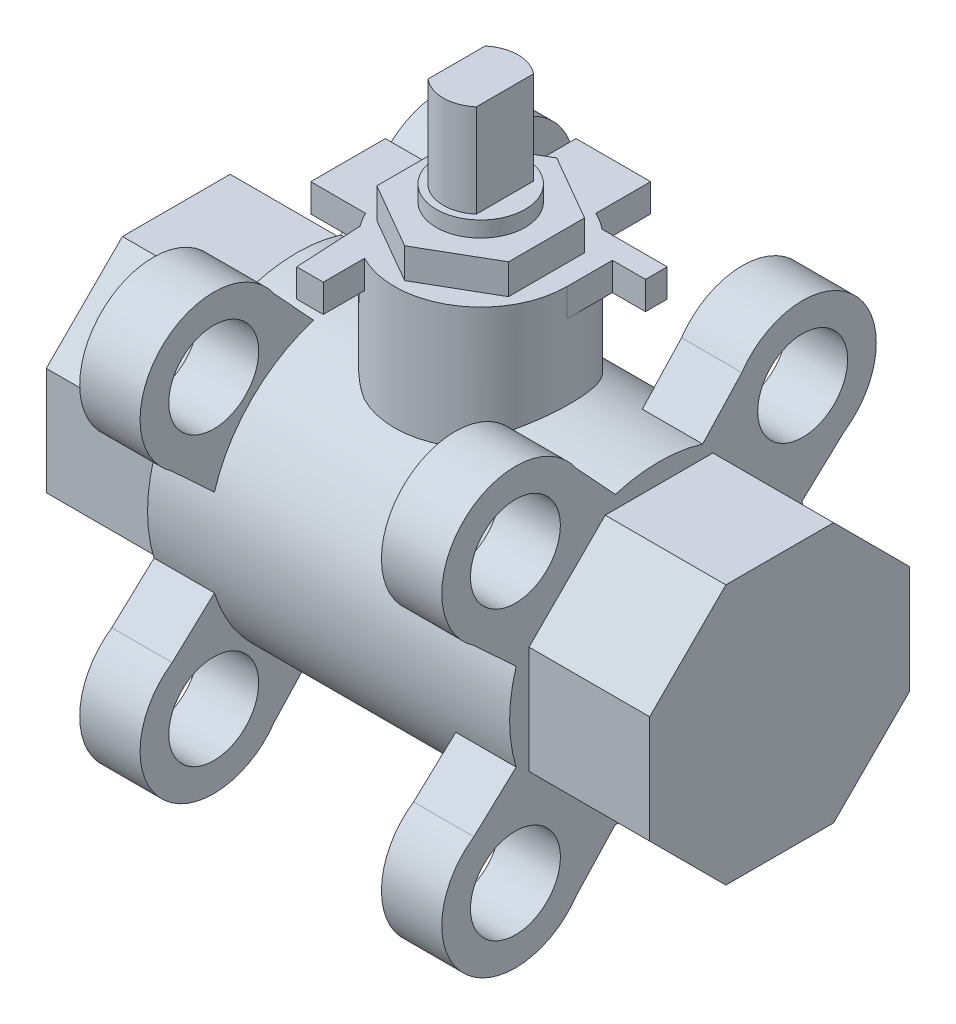
SolidWorks part; units mm, degrees
ref_plane "Front Plane" through (0, 0, 0) normal (0, 0, 1) x (1, 0, 0)
ref_plane "Top Plane" through (0, 0, 0) normal (0, 1, 0) x (1, 0, 0)
ref_plane "Right Plane" through (0, 0, 0) normal (1, 0, 0) x (0, 0, -1)
sketch "Sketch1" plane through (0, 0, 0) normal (1, 0, 0) x (0, 0, -1)
  line L0 (0, 0) -> (0, 26.4768) construction
  line L1 (0, 0) -> (0, -33.4304) construction
  line L2 (-12.3067, 12.3067) -> (-19.0868, 19.0868) construction
  line L3 (-19.4818, 8.7154) -> (-15.0368, 4.5929)
  line L4 (-20.0742, 0) -> (0, 0) construction
  line L5 (0, 0) -> (30.2419, 0) construction
  line L6 (19.4818, 8.7154) -> (15.0368, 4.5929)
  line L7 (8.7154, 19.4818) -> (4.5929, 15.0368)
  line L8 (19.4818, -8.7154) -> (15.0368, -4.5929)
  line L9 (8.7154, -19.4818) -> (4.5929, -15.0368)
  line L10 (-8.7154, 19.4818) -> (-4.5929, 15.0368)
  line L11 (-8.7154, -19.4818) -> (-4.5929, -15.0368)
  line L12 (-19.4818, -8.7154) -> (-15.0368, -4.5929)
  circle A0 centre (-15.113, 15.113) radius 4.7308
  arc A1 (-15.0368, -4.5929) -> (-15.0368, 4.5929) centre (0, 0) cw
  arc A2 (-8.7154, 19.4818) -> (-19.4818, 8.7154) centre (-15.113, 15.113) ccw
  arc A3 (4.5929, 15.0368) -> (-4.5929, 15.0368) centre (0, 0) ccw
  arc A4 (15.0368, -4.5929) -> (15.0368, 4.5929) centre (0, 0) ccw
  circle A5 centre (15.113, 15.113) radius 4.7308
  arc A6 (8.7154, 19.4818) -> (19.4818, 8.7154) centre (15.113, 15.113) cw
  circle A7 centre (15.113, -15.113) radius 4.7307
  arc A8 (8.7154, -19.4818) -> (19.4818, -8.7154) centre (15.113, -15.113) ccw
  arc A9 (4.5929, -15.0368) -> (-4.5929, -15.0368) centre (0, 0) cw
  circle A10 centre (-15.113, -15.113) radius 4.7307
  arc A11 (-8.7154, -19.4818) -> (-19.4818, -8.7154) centre (-15.113, -15.113) cw
  dimension "D3" = 9.4615
  dimension "D4" = 15.7226
  dimension "D5" = 15.494
  dimension "D1" = 15.113
  dimension "D2" = 15.113
  dimension "D6" = 15.0368
  dimension "D7" = 4.445
extrude "Boss-Extrude2" add sketch "Sketch1" along normal blind 6.35
sketch "Sketch2" plane through (0, 0, 0) normal (-1, 0, 0) x (0, 0, 1)
  line L0 (0, 0) -> (13.681, 0) construction
  line L1 (0, 0) -> (-13.681, 0) construction
  line L2 (0, 0) -> (0, 17.7652) construction
  line L3 (13.681, 5.6669) -> (13.681, -5.6669)
  line L4 (13.681, -5.6669) -> (5.6669, -13.681)
  line L5 (-5.6669, -13.681) -> (5.6669, -13.681)
  line L6 (-5.6669, -13.681) -> (-13.681, -5.6669)
  line L9 (13.681, 5.6669) -> (5.6669, 13.681)
  line L10 (-5.6669, 13.681) -> (5.6669, 13.681)
  line L11 (-5.6669, 13.681) -> (-13.681, 5.6669)
  line L12 (-13.681, 5.6669) -> (-13.681, -5.6669)
  point P15 (0, 0)
  dimension "D1" = 11.3337
  dimension "D2" = 13.681
  dimension "D3" = 13.681
  dimension "D4" = 45
  dimension "D5" = 11.3337
  dimension "D6" = 5.6669
extrude "Boss-Extrude3" add sketch "Sketch2" along normal blind 12.7
sketch "Sketch3" plane through (6.35, 0, 0) normal (1, 0, 0) x (0, 0, -1)
  circle A0 centre (0, 0) radius 15.7226
  dimension "D1" = 31.4452
extrude "Boss-Extrude4" add sketch "Sketch3" along normal blind 25.4
sketch "Sketch4" plane through (31.75, 0, 0) normal (1, 0, 0) x (0, 0, -1)
  line L0 (0, 0) -> (0, 32.1291) construction
  line L1 (0, 0) -> (0, -27.7781) construction
  line L2 (-12.3067, 12.3067) -> (-19.0868, 19.0868) construction
  line L3 (-19.4818, 8.7154) -> (-15.0368, 4.5929)
  line L4 (-20.0742, 0) -> (0, 0) construction
  line L5 (0, 0) -> (30.2419, 0) construction
  line L6 (19.4818, 8.7154) -> (15.0368, 4.5929)
  line L7 (8.7154, 19.4818) -> (4.5929, 15.0368)
  line L8 (19.4818, -8.7154) -> (15.0368, -4.5929)
  line L9 (8.7154, -19.4818) -> (4.5929, -15.0368)
  line L10 (-8.7154, 19.4818) -> (-4.5929, 15.0368)
  line L11 (-8.7154, -19.4818) -> (-4.5929, -15.0368)
  line L12 (-19.4818, -8.7154) -> (-15.0368, -4.5929)
  circle A0 centre (-15.113, 15.113) radius 4.7308
  arc A1 (-15.0368, -4.5929) -> (-15.0368, 4.5929) centre (0, 0) cw
  arc A2 (-8.7154, 19.4818) -> (-19.4818, 8.7154) centre (-15.113, 15.113) ccw
  arc A3 (4.5929, 15.0368) -> (-4.5929, 15.0368) centre (0, 0) ccw
  arc A4 (15.0368, -4.5929) -> (15.0368, 4.5929) centre (0, 0) ccw
  circle A5 centre (15.113, 15.113) radius 4.7308
  arc A6 (8.7154, 19.4818) -> (19.4818, 8.7154) centre (15.113, 15.113) cw
  circle A7 centre (15.113, -15.113) radius 4.7307
  arc A8 (8.7154, -19.4818) -> (19.4818, -8.7154) centre (15.113, -15.113) ccw
  arc A9 (4.5929, -15.0368) -> (-4.5929, -15.0368) centre (0, 0) cw
  circle A10 centre (-15.113, -15.113) radius 4.7308
  arc A11 (-8.7154, -19.4818) -> (-19.4818, -8.7154) centre (-15.113, -15.113) cw
  dimension "D1" = 9.4615
  dimension "D2" = 15.494
  dimension "D5" = 15.7226
  dimension "D3" = 15.113
  dimension "D4" = 15.113
  dimension "D6" = 15.0368
  dimension "D7" = 4.445
  dimension "D8" = 0
  dimension "D9" = 0
extrude "Boss-Extrude5" add sketch "Sketch4" along normal blind 6.35
sketch "Sketch5" plane through (38.1, 0, 0) normal (1, 0, 0) x (0, 0, -1)
  line L0 (0, 0) -> (13.681, 0) construction
  line L1 (0, 0) -> (-13.681, 0) construction
  line L2 (0, 0) -> (0, 17.7652) construction
  line L3 (13.681, 5.6669) -> (13.681, -5.6669)
  line L4 (13.681, -5.6669) -> (5.6669, -13.681)
  line L5 (-5.6669, -13.681) -> (5.6669, -13.681)
  line L6 (-5.6669, -13.681) -> (-13.681, -5.6669)
  line L7 (13.681, 5.6669) -> (5.6669, 13.681)
  line L8 (-5.6669, 13.681) -> (5.6669, 13.681)
  line L9 (-5.6669, 13.681) -> (-13.681, 5.6669)
  line L10 (-13.681, 5.6669) -> (-13.681, -5.6669)
  point P12 (2.6974, 0.6715)
  dimension "D1" = 11.3337
  dimension "D2" = 13.681
  dimension "D3" = 13.681
  dimension "D4" = 45
  dimension "D5" = 11.3337
  dimension "D6" = 5.6669
  dimension "D7" = 0
  dimension "D8" = 0
extrude "Boss-Extrude6" add sketch "Sketch5" along normal blind 12.7
sketch "Sketch6" plane through (0, 13.681, 0) normal (0, 1, 0) x (1, 0, 0)
  line L0 (-12.7, 0) -> (50.8, 0.568) construction
  line L1 (-12.7, -5.6669) -> (-12.7, 5.6669) construction
  line L2 (50.8, 5.6669) -> (50.8, -5.6669) construction
  line L3 (19.05, 0.284) -> (19.05, 15.7226) construction
  line L4 (38.1, 15.7226) -> (0, 15.7226) construction
  circle A0 centre (19.05, 0.284) radius 9.0805
  dimension "D1" = 18.161
  dimension "D2" = 15.4386
extrude "Boss-Extrude8" add sketch "Sketch6" along normal blind 12.8778
sketch "Sketch8" plane through (0, 26.5588, 0) normal (0, 1, 0) x (1, 0, 0)
  line L0 (15.1257, 6.1641) -> (15.1257, 14.2413)
  line L1 (13.1699, -3.6403) -> (13.1699, 4.2083)
  line L2 (15.1257, 14.2413) -> (22.9743, 14.2413)
  line L3 (22.9743, 14.2413) -> (22.9743, 6.1641)
  line L4 (22.9743, 6.1641) -> (15.1257, 6.1641)
  line L5 (5.0927, -3.6403) -> (13.1699, -3.6403)
  line L6 (12.6291, 6.7049) -> (19.05, 0.284) construction
  line L7 (5.0927, 4.2083) -> (5.0927, -3.6403)
  line L8 (13.1699, 4.2083) -> (5.0927, 4.2083)
  circle A0 centre (19.05, 0.284) radius 9.0805 construction
  dimension "D1" = 7.8486
  dimension "D2" = 6.4209
  dimension "D3" = 8.0772
  dimension "D4" = 5.8801
  dimension "D5" = 3.9243
extrude "Boss-Extrude9" add sketch "Sketch8" against normal blind 2.9464
sketch "Sketch10" plane through (0, 26.5588, 0) normal (0, 1, 0) x (1, 0, 0)
  line L0 (24.7523, 7.3508) -> (31.6103, 7.3508)
  line L1 (31.6103, 7.3508) -> (31.6103, 5.0648)
  line L2 (28.1305, 0.284) -> (28.1305, 5.0648)
  line L3 (28.1305, 5.0648) -> (31.6103, 5.0648)
  line L6 (11.7439, -5.1083) -> (12.1125, -12.1405)
  line L7 (12.1125, -12.1405) -> (14.9065, -12.1405)
  line L8 (14.9065, -12.1405) -> (14.9065, -7.796)
  arc A0 (14.9065, -7.796) -> (28.1305, 0.284) centre (19.05, 0.284) ccw
  arc A1 (24.7523, 7.3508) -> (11.7439, -5.1083) centre (19.05, 0.284) ccw
  dimension "D1" = 18.161
  dimension "D2" = 6.858
  dimension "D3" = 93
  dimension "D4" = 2.286
  dimension "D5" = 3.4798
  dimension "D6" = 4.3445
  dimension "D7" = 5.3923
  dimension "D8" = 2.794
extrude "Boss-Extrude10" add sketch "Sketch10" against normal blind 2.9464
sketch "Sketch11" plane through (0, 26.5588, 0) normal (0, 1, 0) x (1, 0, 0)
  line L1 (19.05, 8.285) -> (12.1209, 4.2845)
  line L2 (12.1209, 4.2845) -> (12.1209, -3.7165)
  line L3 (12.1209, -3.7165) -> (19.05, -7.717)
  line L4 (19.05, -7.717) -> (25.9791, -3.7165)
  line L5 (25.9791, -3.7165) -> (25.9791, 4.2845)
  line L6 (25.9791, 4.2845) -> (19.05, 8.285)
  circle A1 centre (19.05, 0.284) radius 6.9291 construction
  dimension "D1" = 8.001
  dimension "D2" = 4.0005
extrude "Boss-Extrude11" add sketch "Sketch11" along normal blind 3.175
sketch "Sketch12" plane through (0, 29.7338, 0) normal (0, 1, 0) x (1, 0, 0)
  circle A0 centre (19.05, 0.284) radius 4.6736
  dimension "D1" = 9.3472
extrude "Boss-Extrude12" add sketch "Sketch12" along normal blind 1.651
sketch "Sketch13" plane through (0, 31.3848, 0) normal (0, 1, 0) x (1, 0, 0)
  line L0 (16.51, 3.2921) -> (16.51, -2.724)
  line L1 (19.05, 0.284) -> (19.05, 10.5979) construction
  line L2 (21.59, 3.2921) -> (21.59, -2.724)
  arc A0 (16.51, -2.724) -> (21.59, -2.724) centre (19.05, 0.284) ccw
  arc A1 (21.59, 3.2921) -> (16.51, 3.2921) centre (19.05, 0.284) ccw
  dimension "D1" = 7.874
  dimension "D2" = 2.54
extrude "Boss-Extrude13" add sketch "Sketch13" along normal blind 9.779
